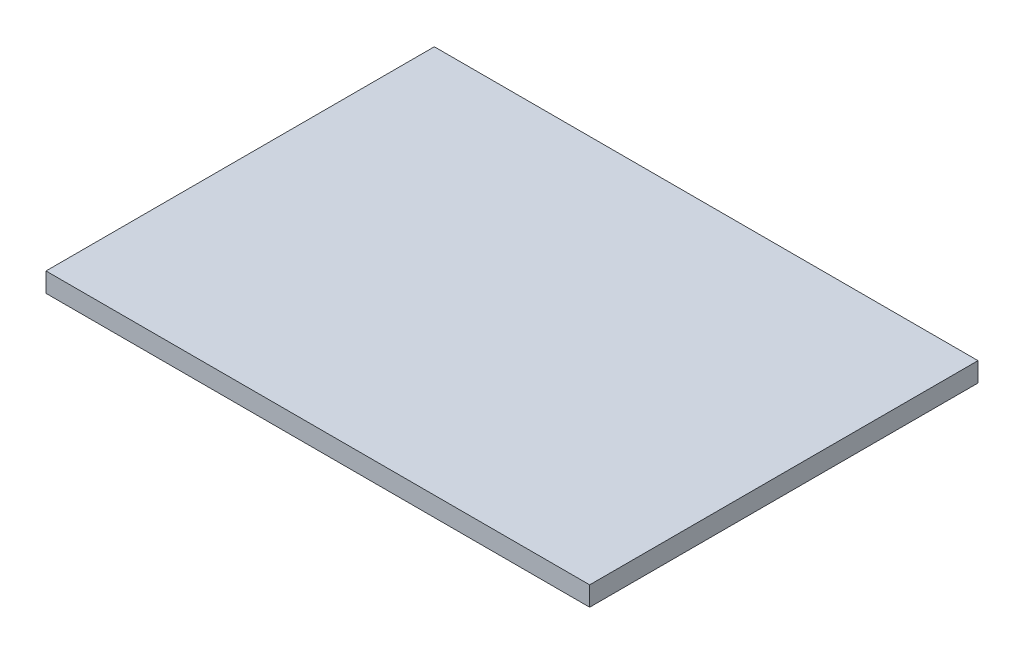
SolidWorks part; units mm, degrees
ref_plane "Front Plane" through (0, 0, 0) normal (0, 0, 1) x (1, 0, 0)
ref_plane "Top Plane" through (0, 0, 0) normal (0, 1, 0) x (1, 0, 0)
ref_plane "Right Plane" through (0, 0, 0) normal (1, 0, 0) x (0, 0, -1)
sketch "Sketch1" plane through (0, 0, 0) normal (0, 1, 0) x (1, 0, 0)
  line L1 (-177.8, 127) -> (177.8, 127)
  line L2 (-177.8, 127) -> (-177.8, -127)
  line L3 (-177.8, -127) -> (177.8, -127)
  line L4 (177.8, 127) -> (177.8, -127)
  line L5 (-177.8, 127) -> (177.8, -127) construction
  line L6 (-177.8, -127) -> (177.8, 127) construction
  point P0 (0, 0)
  dimension "D1" = 355.6
  dimension "D2" = 254
extrude "Boss-Extrude1" add sketch "Sketch1" along normal blind 12.7
